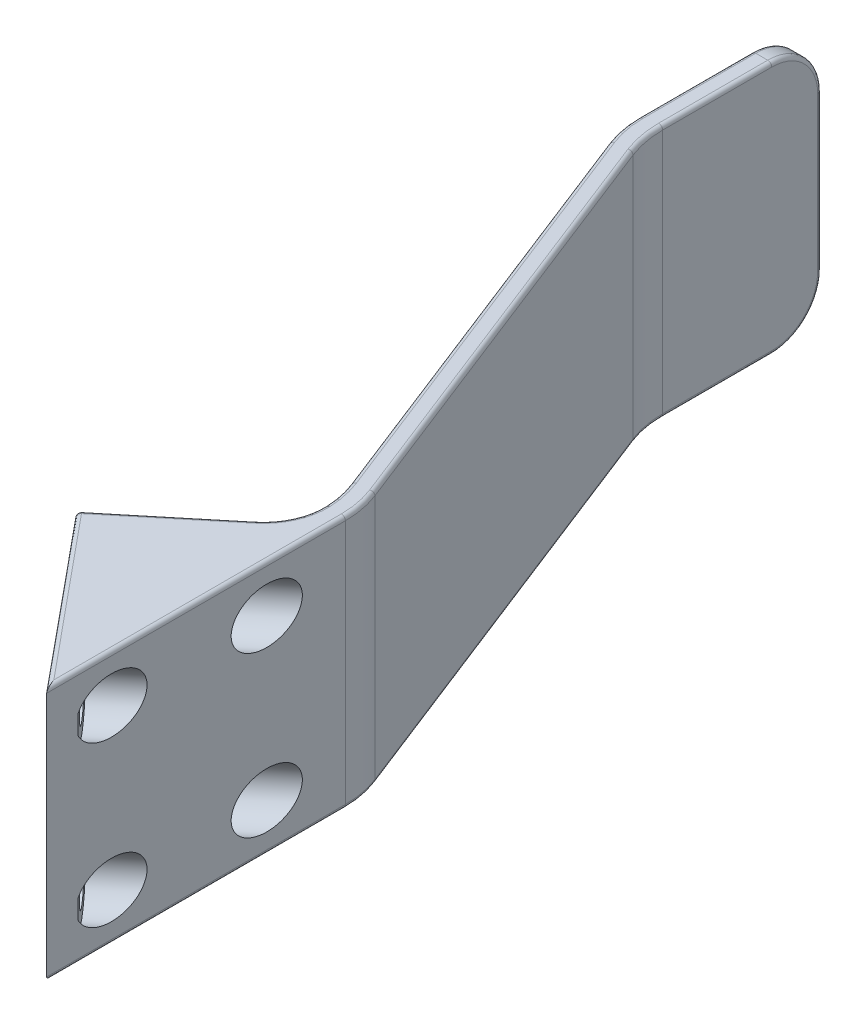
SolidWorks part; units mm, degrees
ref_plane "Front Plane" through (0, 0, 0) normal (0, 0, 1) x (1, 0, 0)
ref_plane "Top Plane" through (0, 0, 0) normal (0, 1, 0) x (1, 0, 0)
ref_plane "Right Plane" through (0, 0, 0) normal (1, 0, 0) x (0, 0, -1)
sketch "Sketch1" plane through (0, 0, 0) normal (0, 0, 1) x (1, 0, 0)
  line L0 (0, 0) -> (0, 24.7759) construction
  line L1 (0, 0) -> (34.3441, 0) construction
  line L3 (21, 12.7) -> (23, 12.7)
  line L4 (21, 12.7) -> (21, -12.7)
  line L5 (21, -12.7) -> (23, -12.7)
  line L6 (23, 12.7) -> (23, -12.7)
  line L7 (21, 12.7) -> (23, -12.7) construction
  line L8 (21, -12.7) -> (23, 12.7) construction
  point P3 (22, 0)
  dimension "D1" = 21
  dimension "D2" = 2
  dimension "D3" = 25.4
sketch "Sketch2" plane through (0, 0, 0) normal (0, 1, 0) x (1, 0, 0)
  line L0 (22, 0) -> (22, 57.2)
  line L1 (22, 57.2) -> (4, 103.2)
  line L2 (4, 103.2) -> (4, 121.2)
  line L3 (0, 0) -> (0, 51.9607) construction
  dimension "D1" = 4
  dimension "D2" = 18
  dimension "D3" = 121.2
  dimension "D4" = 64
sweep "Sweep1" add profiles "Sketch1" path "Sketch2"
sketch "Sketch4" plane through (23, 0, 0) normal (1, 0, 0) x (0, 0, -1)
  line L0 (57.3887, -12.7) -> (0, -12.7) construction
  line L1 (0, 12.7) -> (5, 12.7)
  line L2 (0, 12.7) -> (0, -12.7)
  line L3 (0, -12.7) -> (5, -12.7)
  line L4 (5, 12.7) -> (5, -12.7)
  dimension "D1" = 5
extrude "Cut-Extrude2" cut sketch "Sketch4" against normal through all
sketch "Sketch5" plane through (0, -12.7, 0) normal (0, -1, 0) x (1, 0, 0)
  line L0 (21, -42.5613) -> (21, -28.0151)
  line L3 (21, -42.5613) -> (9, -42.5613)
  line L5 (9, -42.5613) -> (21, -28.0151)
  line L8 (21, -57.0113) -> (21, -5) construction
  dimension "D1" = 18.8571
  dimension "D2" = 14.45
  dimension "D3" = 12
extrude "Boss-Extrude2" add sketch "Sketch5" against normal through all
sketch "Sketch6" plane through (0, -12.7, 0) normal (0, -1, 0) x (1, 0, 0)
  line L0 (9, -42.5613) -> (21, -52.4608)
  line L1 (21, -57.0113) -> (21, -42.5613) construction
  line L2 (21, -52.4608) -> (21, -42.5613)
  line L3 (21, -42.5613) -> (9, -42.5613)
  line L4 (21, -28.0151) -> (9, -42.5613) construction
extrude "Boss-Extrude4" add sketch "Sketch6" against normal through all
fillet "Fillet1" radius 5 2 edges at (4, -12.7, -121.2) (4, 12.7, -121.2)
sketch "Sketch8" plane through (0, -12.7, 0) normal (0, -1, 0) x (1, 0, 0)
  line L2 (23, -25.5908) -> (23, -5)
  line L3 (23, -5) -> (21, -5)
  line L4 (21, -5) -> (21, -28.0151)
  line L5 (21, -28.0151) -> (9, -42.5613) construction
  line L6 (21, -28.0151) -> (23, -25.5908)
extrude "Cut-Extrude3" cut sketch "Sketch8" against normal through all
sketch "Sketch9" plane through (26.248, 0, -21.6535) normal (-0.7714, 0, 0.6364) x (0.6364, 0, 0.7714)
  line L0 (-16.1041, 12.7) -> (-16.1041, -12.7) construction
  line L3 (-27.1041, 0) -> (-5.1041, 0) construction
  line L4 (-27.1041, 12.7) -> (-27.1041, -12.7) construction
  line L5 (-5.1041, 12.7) -> (-5.1041, -12.7) construction
  circle A0 centre (-22.1041, 8) radius 1.6
  circle A1 centre (-22.1041, -8) radius 1.6
  circle A2 centre (-10.1041, -8) radius 1.6
  circle A3 centre (-10.1041, 8) radius 1.6
  circle A4 centre (-22.1041, 8) radius 2.75 construction
  dimension "D1" = 3.2
  dimension "D2" = 5.5
  dimension "D3" = 12
  dimension "D4" = 16
  dimension "D5" = 11
extrude "Cut-Extrude4" cut sketch "Sketch9" against normal blind 2
sketch "Sketch10" plane through (27.7908, 0, -22.9263) normal (-0.7714, 0, 0.6364) x (0.6364, 0, 0.7714)
  circle A0 centre (-22.1041, 8) radius 2.75
  circle A1 centre (-10.1041, 8) radius 2.75
  circle A2 centre (-10.1041, -8) radius 2.75
  circle A3 centre (-22.1041, -8) radius 2.75
  dimension "D1" = 5.5
extrude "Cut-Extrude5" cut sketch "Sketch10" against normal through all
sketch "Sketch11" plane through (0, -12.7, 0) normal (0, -1, 0) x (1, 0, 0)
  line L0 (9, -42.5613) -> (18.4756, -31.0751) construction
  line L1 (23, -25.5908) -> (9, -42.5613) construction
  line L2 (18.4756, -31.0751) -> (23, -34.8075)
  line L3 (23, -57.3887) -> (23, -25.5908) construction
  line L4 (23, -34.8075) -> (23, -25.5908)
  line L5 (23, -25.5908) -> (18.4756, -31.0751)
  dimension "D1" = 14.8903
extrude "Cut-Extrude6" [suppressed] cut sketch "Sketch11" against normal through all
fillet "Fillet2" radius 10 4 edges at (5, 0, -103.3887) (3, 0, -103.0113) (21, 0, -57.0113) (23, 0, -57.3887)
fillet "Fillet5" radius 6 1 edges at (21, 0, -52.4608)
fillet "Fillet3" radius 0.4 31 edges at (5, -12.7, -110.7378) (5, 12.7, -110.7378) (14, 12.7, -80.3887) (14, -12.7, -80.3887) (3, -12.7, -110.5491) (3, 12.7, -110.5491) (23, 12.7, -40.5463) (12, 12.7, -80.0113) (22.8266, 12.7, -57.356) (3.1734, 12.7, -103.044) (12, -12.7, -80.0113) (23, -12.7, -40.5463) (22.8266, -12.7, -57.356) (3.1734, -12.7, -103.044) (5.1734, -12.7, -103.4214) (5.1734, 12.7, -103.4214) (20.787, 12.7, -57.1773) (20.787, -12.7, -57.1773) (20.4746, -12.7, -52.8386) (20.4746, 12.7, -52.8386) (16, 12.7, -34.076) (9, 0, -42.5613) (16, -12.7, -34.076) (13.9074, 12.7, -46.6098) (13.9074, -12.7, -46.6098) (5, 0, -121.2) (5, 11.2355, -119.7355) (5, -11.2355, -119.7355) (3, 0, -121.2) (3, 11.2355, -119.7355) (3, -11.2355, -119.7355)
fillet "Fillet6" [suppressed] radius 0.6
